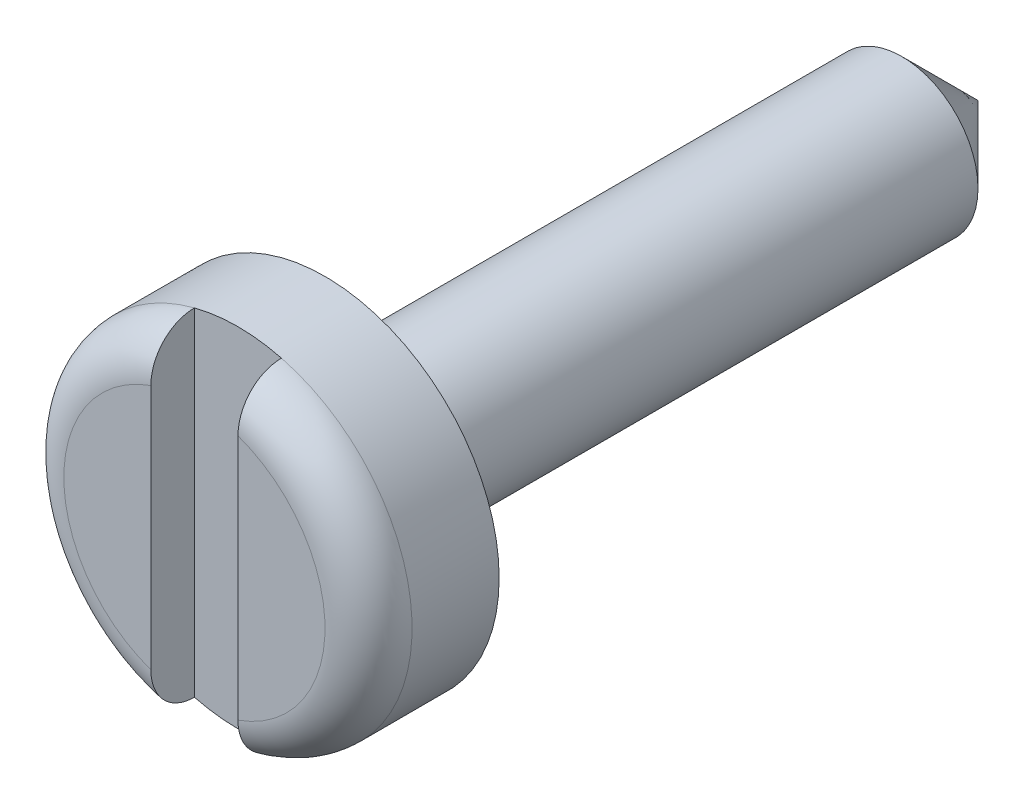
SolidWorks part; units mm, degrees
ref_plane "Přední rovina" through (0, 0, 0) normal (0, 0, 1) x (1, 0, 0)
ref_plane "Horní rovina" through (0, 0, 0) normal (0, 1, 0) x (1, 0, 0)
ref_plane "Pravá rovina" through (0, 0, 0) normal (1, 0, 0) x (0, 0, -1)
sketch "Skica1" plane through (0, 0, 0) normal (0, 0, 1) x (1, 0, 0)
  circle A0 centre (0, 0) radius 1.75
extrude "Vysunout1" add sketch "Skica1" along normal blind 15
sketch "Skica3" plane through (0, 0, 15) normal (0, 0, 1) x (1, 0, 0)
  circle A0 centre (0, 0) radius 4
  point P0 (0, 0)
extrude "Vysunout2" add sketch "Skica3" along normal blind 3
fillet "Zaoblit1" radius 1 1 edges at (4, 0, 18)
chamfer "Zkosit1" distance 1.75 angle 45 1 edges at (1.75, 0, 0)
sketch "Skica8" plane through (0, 0, 18) normal (0, 0, 1) x (1, 0, 0)
  line L0 (0, -3) -> (0, 3) construction
  line L1 (0, -4) -> (0, 4) construction
  line L2 (-1, -4) -> (1, -4)
  line L3 (-1, -4) -> (-1, 4)
  line L4 (-1, 4) -> (1, 4)
  line L5 (1, -4) -> (1, 4)
  circle A0 centre (0, 0) radius 3 construction
  point P11 (0, 0)
  point P12 (0, 0)
  dimension "D1" = 2
  dimension "D2" = 8
extrude "Odebrat vysunutím2" cut sketch "Skica8" against normal blind 1
